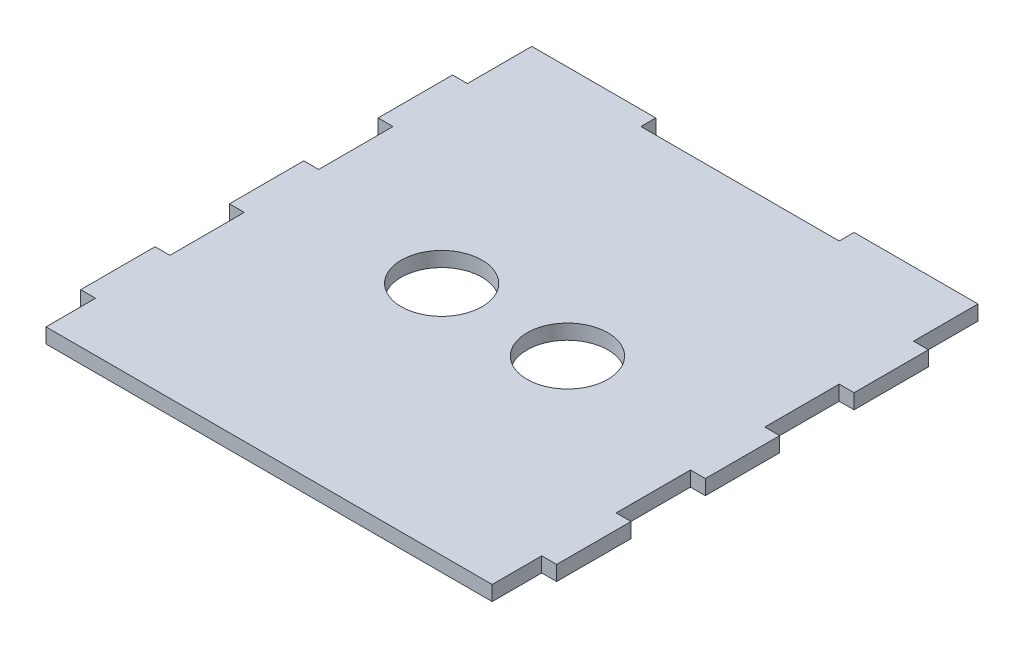
SolidWorks part; units mm, degrees
ref_plane "Front" through (0, 0, 0) normal (0, 0, 1) x (1, 0, 0)
ref_plane "Top" through (0, 0, 0) normal (0, 1, 0) x (1, 0, 0)
ref_plane "Right" through (0, 0, 0) normal (1, 0, 0) x (0, 0, -1)
sketch "Sketch1" plane through (0, 0, 0) normal (0, 1, 0) x (1, 0, 0)
  line L0 (0, 47.5) -> (90, 47.5) construction
  line L1 (0, 0) -> (90, 0)
  line L2 (0, 0) -> (0, 95)
  line L3 (0, 95) -> (90, 95)
  line L4 (90, 0) -> (90, 95)
  line L5 (45, 95) -> (45, 0) construction
  dimension "D1" = 90
  dimension "D7" = 95
extrude "Boss-Extrude1" add sketch "Sketch1" along normal blind 3
sketch "Sketch2" [suppressed] plane through (0, 3, 0) normal (0, 1, 0) x (1, 0, 0)
  line L1 (27.5, 98) -> (62.5, 98)
  line L2 (27.5, 98) -> (27.5, 95)
  line L3 (27.5, 95) -> (62.5, 95)
  line L4 (62.5, 98) -> (62.5, 95)
  dimension "D1" = 3
  dimension "D2" = 35
extrude "Boss-Extrude2" [suppressed] add sketch "Sketch2" against normal blind 3
sketch "Sketch3" [suppressed] plane through (0, 3, 0) normal (0, 1, 0) x (1, 0, 0)
  line L1 (-3, 67.5) -> (0, 67.5)
  line L2 (-3, 67.5) -> (-3, 27.5)
  line L3 (-3, 27.5) -> (0, 27.5)
  line L4 (0, 67.5) -> (0, 27.5)
  line L5 (90, 27.5) -> (93, 27.5)
  line L6 (90, 27.5) -> (90, 67.5)
  line L7 (90, 67.5) -> (93, 67.5)
  line L8 (93, 27.5) -> (93, 67.5)
  dimension "D1" = 40
  dimension "D2" = 3
  dimension "D3" = 3
extrude "Boss-Extrude3" [suppressed] add sketch "Sketch3" against normal blind 3
sketch "Sketch4" plane through (0, 3, 0) normal (0, 1, 0) x (1, 0, 0)
  line L0 (0, 0) -> (0, 95) construction
  line L1 (-3, 85) -> (0, 85)
  line L2 (-3, 85) -> (-3, 70)
  line L3 (-3, 70) -> (0, 70)
  line L4 (0, 85) -> (0, 70)
  line L5 (-3, 55) -> (0, 55)
  line L6 (-3, 55) -> (-3, 40)
  line L7 (-3, 40) -> (0, 40)
  line L8 (0, 55) -> (0, 40)
  line L9 (-3, 25) -> (0, 25)
  line L10 (-3, 25) -> (-3, 10)
  line L11 (-3, 10) -> (0, 10)
  line L12 (0, 25) -> (0, 10)
  line L13 (90, 85) -> (93, 85)
  line L14 (90, 85) -> (90, 70)
  line L15 (90, 70) -> (93, 70)
  line L16 (93, 85) -> (93, 70)
  line L17 (90, 55) -> (93, 55)
  line L18 (90, 55) -> (90, 40)
  line L19 (90, 40) -> (93, 40)
  line L20 (93, 55) -> (93, 40)
  line L21 (90, 25) -> (93, 25)
  line L22 (90, 25) -> (90, 10)
  line L23 (90, 10) -> (93, 10)
  line L24 (93, 25) -> (93, 10)
  line L25 (90, 0) -> (90, 95) construction
  line L26 (0, 0) -> (90, 0) construction
  line L28 (0, 95) -> (90, 95) construction
  line L29 (45, 95) -> (45, 0) construction
  point P34 (-3, 47.5)
  point P35 (45, 47.5)
  dimension "D2" = 3
  dimension "D1" = 3
  dimension "D3" = 15
  dimension "D4" = 15
  dimension "D5" = 15
  dimension "D6" = 10
  dimension "D7" = 95
  dimension "D8" = 10
extrude "Boss-Extrude4" add sketch "Sketch4" against normal blind 3
sketch "Sketch5" plane through (0, 3, 0) normal (0, 1, 0) x (1, 0, 0)
  line L1 (0, 98) -> (90, 98)
  line L2 (0, 98) -> (0, 95)
  line L3 (0, 95) -> (90, 95)
  line L4 (90, 98) -> (90, 95)
  dimension "D1" = 3
extrude "Boss-Extrude5" add sketch "Sketch5" against normal blind 3
sketch "Sketch6" plane through (0, 3, 0) normal (0, 1, 0) x (1, 0, 0)
  line L1 (25, 98) -> (65, 98)
  line L2 (25, 98) -> (25, 95)
  line L3 (25, 95) -> (65, 95)
  line L4 (65, 98) -> (65, 95)
  line L5 (0, 0) -> (90, 0) construction
  point P4 (45, 98)
  dimension "D1" = 3
  dimension "D2" = 40
  dimension "D3" = 95
extrude "Cut-Extrude2" cut sketch "Sketch6" against normal blind 4
sketch "Sketch7" [suppressed] plane through (0, 3, 0) normal (0, 1, 0) x (1, 0, 0)
  line L1 (0, 0) -> (90, 0)
  line L2 (0, 0) -> (0, -4)
  line L3 (0, -4) -> (90, -4)
  line L4 (90, 0) -> (90, -4)
  dimension "D1" = 4
extrude "Boss-Extrude6" [suppressed] add sketch "Sketch7" against normal blind 3
sketch "Sketch8" plane through (0, 3, 0) normal (0, 1, 0) x (1, 0, 0)
  line L0 (45, 95) -> (45, 0) construction
  line L1 (25, 95) -> (65, 95) construction
  line L2 (0, 0) -> (90, 0) construction
  line L3 (32.31, 47.5) -> (57.69, 47.5) construction
  circle A0 centre (32.31, 47.5) radius 8.15
  circle A1 centre (57.69, 47.5) radius 8.15
  point P9 (45, 47.5)
  dimension "D3" = 16.3
  dimension "D2" = 16.3
  dimension "D1" = 25.38
extrude "Cut-Extrude3" cut sketch "Sketch8" against normal through all
equation "\"D3@Sketch3\"=\"D2@Sketch3\""
equation "\"D2@Sketch4\"=\"D1@Sketch4\""
equation "\"D4@Sketch4\"=\"D5@Sketch4\""
equation "\"D3@Sketch4\"=\"D5@Sketch4\""
equation "\"D2@Sketch8\"=\"D3@Sketch8\""
